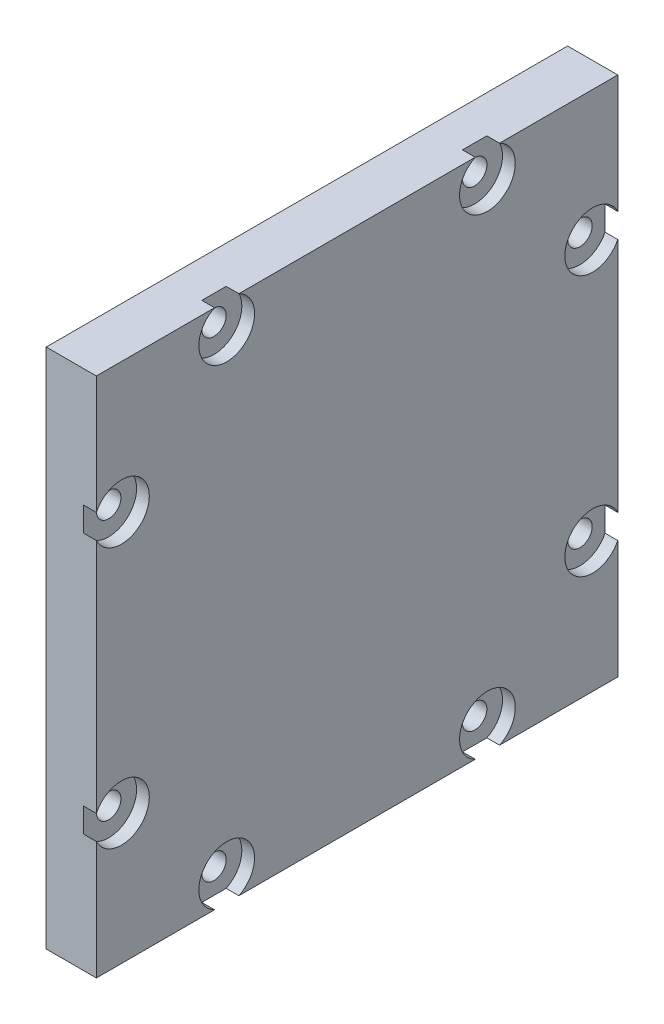
SolidWorks part; units mm, degrees
ref_plane "Front Plane" through (0, 0, 0) normal (0, 0, 1) x (1, 0, 0)
ref_plane "Top Plane" through (0, 0, 0) normal (0, 1, 0) x (1, 0, 0)
ref_plane "Right Plane" through (0, 0, 0) normal (1, 0, 0) x (0, 0, -1)
sketch "Sketch1" plane through (0, 0, 0) normal (1, 0, 0) x (0, 0, -1)
  line L1 (0, 0) -> (52, 0)
  line L2 (0, 0) -> (0, 52)
  line L3 (0, 52) -> (52, 52)
  line L4 (52, 0) -> (52, 52)
extrude "Boss-Extrude1" add sketch "Sketch1" along normal blind 5
sketch "Sketch2" plane through (5, 0, 0) normal (1, 0, 0) x (0, 0, -1)
  line L0 (0, 52) -> (0, 47)
  line L1 (0, 52) -> (0, 0) construction
  line L3 (52, 0) -> (52, 52) construction
  line L4 (52, 47) -> (26, 52)
  line L5 (52, 52) -> (0, 52) construction
  line L6 (26, 52) -> (0, 47)
  line L7 (0, 0) -> (0, 5)
  line L8 (0, 5) -> (26, 0)
  line L9 (0, 0) -> (52, 0) construction
  line L10 (26, 0) -> (52, 5)
  line L11 (0, 52) -> (5, 52)
  line L12 (5, 52) -> (0, 26)
  line L13 (0, 26) -> (5, 0)
  line L14 (52, 52) -> (47, 52)
  line L15 (47, 52) -> (52, 26)
  line L16 (52, 26) -> (47, 0)
  point P26 (52, 47)
  point P27 (45.8875, 52)
  point P28 (48.6576, 52)
  point P29 (47, 0)
  point P30 (52, 5)
  point P31 (6.4676, 0)
  point P32 (5, 0)
hole_wizard "CBORE for #2 Binding Head Machine Screw1" positions "Sketch7" profile "Sketch8" counterbore size "#2" standard "ANSI Inch" end condition through all
sketch "Sketch7" plane through (5, 0, 0) normal (1, 0, 0) x (0, 0, -1)
  line L0 (26, 52) -> (0, 47) construction
  line L1 (52, 47) -> (26, 52) construction
  line L2 (47, 52) -> (52, 26) construction
  line L3 (52, 26) -> (47, 0) construction
  line L4 (26, 0) -> (52, 5) construction
  line L5 (0, 5) -> (26, 0) construction
  line L6 (0, 26) -> (5, 0) construction
  line L7 (5, 52) -> (0, 26) construction
  point P0 (13, 49.5)
  point P4 (39, 49.5)
  point P8 (49.5, 39)
  point P12 (49.5, 13)
  point P16 (39, 2.5)
  point P20 (13, 2.5)
  point P24 (2.5, 13)
  point P28 (2.5, 39)
sketch "Sketch8" plane through (5, 49.5, -13) normal (0, 1, 0) x (0, 0, -1)
  line L0 (0, 0) -> (0, 5)
  line L1 (0, 5) -> (1.2192, 5)
  line L3 (1.2192, 5) -> (1.2192, 1.27)
  line L4 (1.2192, 1.27) -> (2.7788, 1.27)
  line L5 (2.7788, 1.27) -> (2.7788, 0)
  line L7 (2.7788, 0) -> (0, 0)
  line L11 (0, -6.35) -> (0, 107.95) construction
  dimension "Thru Hole Dia." = 2.4384
  dimension "Thru Hole Depth" = 5
  dimension "C'Bore Dia." = 5.5575
  dimension "C'Bore Depth" = 1.27
